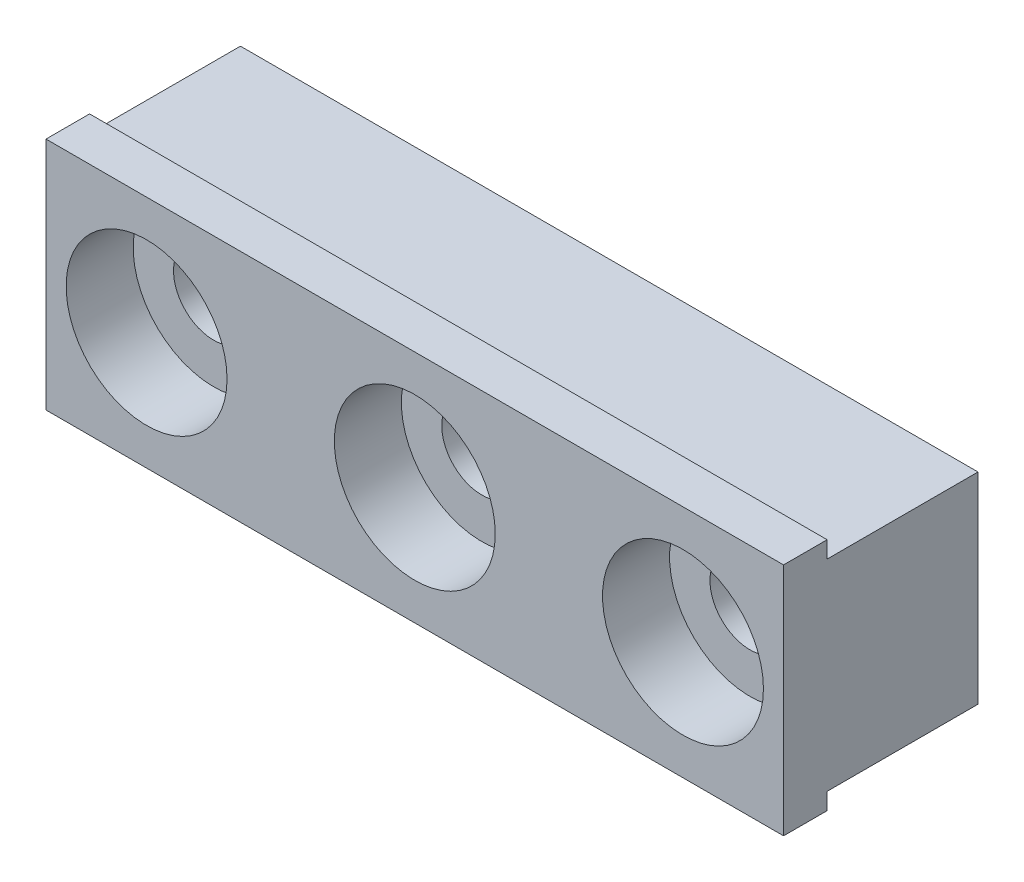
SolidWorks part; units mm, degrees
material "PVC Rigid"
ref_plane "Front Plane" through (0, 0, 0) normal (0, 0, 1) x (1, 0, 0)
ref_plane "Top Plane" through (0, 0, 0) normal (0, 1, 0) x (1, 0, 0)
ref_plane "Right Plane" through (0, 0, 0) normal (1, 0, 0) x (0, 0, -1)
sketch "Sketch1" plane through (0, 0, 0) normal (0, 0, 1) x (1, 0, 0)
  line L1 (0, 0) -> (34.925, 0)
  line L2 (0, 0) -> (0, 9.525)
  line L3 (0, 9.525) -> (34.925, 9.525)
  line L4 (34.925, 0) -> (34.925, 9.525)
  dimension "D1" = 9.525
  dimension "D2" = 34.925
extrude "Boss-Extrude1" add sketch "Sketch1" along normal blind 7.1437
sketch "Sketch2" plane through (0, 0, 7.1437) normal (0, 0, 1) x (1, 0, 0)
  line L0 (34.925, 0) -> (34.925, 9.525) construction
  line L1 (0, 10.3187) -> (34.925, 10.3187)
  line L2 (0, 10.3187) -> (0, -0.7937)
  line L3 (0, -0.7937) -> (34.925, -0.7937)
  line L4 (34.925, 10.3187) -> (34.925, -0.7937)
  line L5 (0, 9.525) -> (0, 0) construction
  line L11 (0, 0) -> (34.925, 0) construction
  dimension "D1" = 11.1125
  dimension "D2" = 0.7937
extrude "Boss-Extrude2" add sketch "Sketch2" along normal blind 2.0638
hole_wizard "#6 Clearance Hole1" positions "Sketch3" profile "Sketch4" hole size "#6" standard "ANSI Inch" end condition up to next
sketch "Sketch3" plane through (0, 0, 9.2075) normal (0, 0, 1) x (1, 0, 0)
  line L0 (0, 4.7625) -> (34.925, 4.7625) construction
  line L1 (0, 10.3187) -> (0, -0.7937) construction
  line L2 (34.925, -0.7937) -> (34.925, 10.3187) construction
  point P0 (4.7625, 4.7625)
  point P2 (17.4625, 4.7625)
  point P4 (30.1625, 4.7625)
  dimension "D1" = 12.7
  dimension "D2" = 12.7
sketch "Sketch4" plane through (4.7625, 4.7625, 9.2075) normal (1, 0, 0) x (0, -1, 0)
  line L0 (0, 0) -> (0, 9.2075)
  line L1 (0, 9.2075) -> (1.8986, 9.2075)
  line L2 (1.8986, 9.2075) -> (1.8986, 0)
  line L5 (1.8986, 0) -> (0, 0)
  line L11 (0, -6.35) -> (0, 107.95) construction
  dimension "Thru Hole Dia." = 3.7973
  dimension "Thru Hole Depth" = 9.2075
sketch "Sketch5" plane through (0, 0, 9.2075) normal (0, 0, 1) x (1, 0, 0)
  circle A0 centre (4.7625, 4.7625) radius 3.81
  circle A1 centre (17.4625, 4.7625) radius 3.81
  circle A2 centre (30.1625, 4.7625) radius 3.81
  dimension "D1" = 7.62
extrude "Cut-Extrude1" cut sketch "Sketch5" against normal blind 3.175
